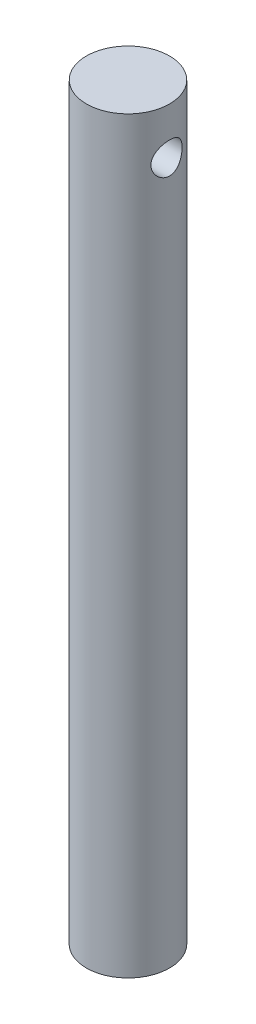
SolidWorks part; units mm, degrees
material "1060 Alloy"
ref_plane "Front" through (0, 0, 0) normal (0, 0, 1) x (1, 0, 0)
ref_plane "Top" through (0, 0, 0) normal (0, 1, 0) x (1, 0, 0)
ref_plane "Right" through (0, 0, 0) normal (1, 0, 0) x (0, 0, -1)
sketch "Sketch1" plane through (0, 0, 0) normal (0, 1, 0) x (1, 0, 0)
  circle A0 centre (0, 0) radius 2
  dimension "D1" = 4
extrude "Boss-Extrude1" add sketch "Sketch1" along normal blind 36
sketch "Sketch2" plane through (0, 0, 0) normal (1, 0, 0) x (0, 0, -1)
  line L0 (2, 36) -> (-2, 36) construction
  circle A0 centre (0, 33.75) radius 0.75
  dimension "D1" = 1.5
  dimension "D2" = 1.5
extrude "Cut-Extrude1" cut sketch "Sketch2" against normal mid plane 36
